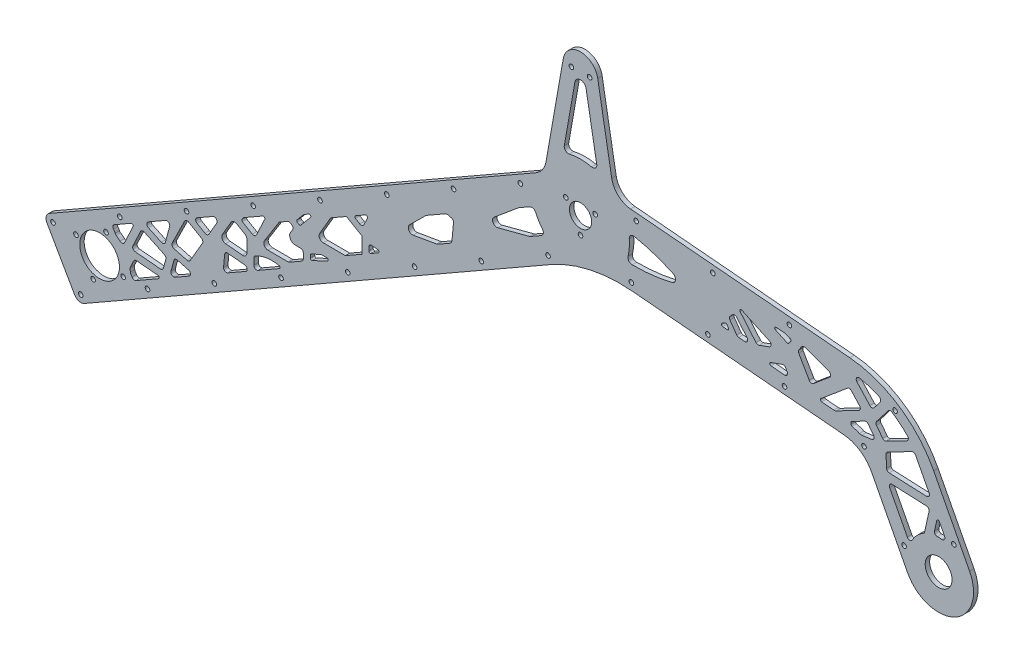
SolidWorks part; units mm, degrees
material "6061-T6 (SS)"
ref_plane "Front Plane" through (0, 0, 0) normal (0, 0, 1) x (1, 0, 0)
ref_plane "Top Plane" through (0, 0, 0) normal (0, 1, 0) x (1, 0, 0)
ref_plane "Right Plane" through (0, 0, 0) normal (1, 0, 0) x (0, 0, -1)
sketch "Reference Sketch" plane through (0, 0, 0) normal (0, 0, 1) x (1, 0, 0)
  line L0 (-343.92, -196.825) -> (0, 0) construction
  line L1 (-243.92, 103.175) -> (356.08, 103.175) construction
  line L2 (-243.92, 103.175) -> (-243.92, 0) construction
  line L3 (-243.92, 0) -> (356.08, 0) construction
  line L4 (356.08, 103.175) -> (356.08, 0) construction
  line L5 (0, 0) -> (256.08, -92.7116) construction
  line L6 (256.08, -92.7116) -> (56.08, -196.825) construction
  line L7 (256.08, -92.7116) -> (456.08, -196.825) construction
  line L8 (-343.92, -196.825) -> (56.08, -196.825) construction
  line L9 (56.08, -196.825) -> (456.08, -196.825) construction
  circle A1 centre (-343.92, -196.825) radius 100 construction
  circle A2 centre (56.08, -196.825) radius 100 construction
  circle A3 centre (456.08, -196.825) radius 100 construction
  circle A4 centre (-343.92, -196.825) radius 16.05 construction
  circle A5 centre (-343.92, -196.825) radius 28.55 construction
  circle A6 centre (-343.92, -196.825) radius 38.55 construction
  circle A7 centre (-343.92, -196.825) radius 33.55 construction
  point P13 (-343.92, -296.825)
  point P14 (556.08, -196.825)
  point P17 (-443.92, -196.825)
  dimension "D3" = 32.1
  dimension "D5" = 200
  dimension "D9" = 57.1
  dimension "D10" = 10
  dimension "D11" = 5
  dimension "D1" = 600
  dimension "D2" = 103.175
  dimension "D4" = 243.92
  dimension "D6" = 125
  dimension "D7" = 400
  dimension "D8" = 1000
  dimension "D12" = 356.08
sketch "Sketch2" plane through (0, 0, 0) normal (0, 0, 1) x (1, 0, 0)
  line L0 (-379.7168, -188.5069) -> (-32.0065, 10.4873)
  line L1 (-354.8814, -231.9028) -> (-21.5627, -41.1449)
  line L2 (-343.92, -196.825) -> (0, 0) construction
  line L3 (-184.3777, -76.7146) -> (-159.5423, -120.1104) construction
  line L4 (-24.685, 20.9013) -> (-12.3101, 91.0831)
  line L5 (12.3101, 91.0831) -> (22.322, 34.3028)
  line L6 (0, 98.4125) -> (0, 112.7) construction
  line L7 (-5.4848, 79.4125) -> (5.4848, 79.4125) construction
  line L8 (5.4848, 79.4125) -> (10.9697, 88.9125) construction
  line L9 (10.9697, 88.9125) -> (5.4848, 98.4125) construction
  line L10 (5.4848, 98.4125) -> (-5.4848, 98.4125) construction
  line L11 (-5.4848, 98.4125) -> (-10.9697, 88.9125) construction
  line L12 (-10.9697, 88.9125) -> (-5.4848, 79.4125) construction
  line L13 (-243.92, 103.175) -> (356.08, 103.175) construction
  line L14 (0, 88.9125) -> (0, 0) construction
  line L15 (35.7868, 21.9646) -> (192.5861, 8.2464)
  line L16 (252.5753, -31.8371) -> (278.2553, -81.1679)
  line L17 (233.9047, -104.2553) -> (208.2247, -54.9245)
  line L18 (36.8237, -28.3172) -> (188.2284, -41.5633)
  line L19 (0, 0) -> (192.5861, -16.8491) construction
  line L21 (-360.8064, -192.2315) -> (-339.3265, -179.9386) construction
  line L22 (-381.5729, -195.33) -> (-361.7045, -230.0467)
  line L23 (256.08, -92.7116) -> (56.08, -196.825) construction
  line L25 (-243.92, 0) -> (356.08, 0) construction
  circle A0 centre (0, 0) radius 7.9375
  circle A1 centre (-343.92, -196.825) radius 14.2
  arc A3 (-12.3101, 91.0831) -> (12.3101, 91.0831) centre (0, 88.9125) cw
  circle A4 centre (0, 88.9125) radius 6.5 construction
  circle A5 centre (-6.5, 88.9125) radius 1.65
  circle A6 centre (6.5, 88.9125) radius 1.65
  circle A7 centre (0, 88.9125) radius 9.5 construction
  arc A8 (252.5753, -31.8371) -> (192.5861, 8.2464) centre (186.0495, -66.4682) ccw
  circle A9 centre (256.08, -92.7116) radius 9.5885
  arc A10 (278.2553, -81.1679) -> (233.9047, -104.2553) centre (256.08, -92.7116) cw
  arc A11 (-21.5627, -41.1449) -> (36.8237, -28.3172) centre (28.1082, -127.9366) cw
  arc A12 (188.2284, -41.5633) -> (208.2247, -54.9245) centre (186.0495, -66.4682) cw
  arc A13 (22.322, 34.3028) -> (35.7868, 21.9646) centre (37.0941, 36.9075) ccw
  arc A14 (-32.0065, 10.4873) -> (-24.685, 20.9013) centre (-39.4572, 23.506) ccw
  circle A17 centre (-343.92, -196.825) radius 17.5 construction
  circle A18 centre (-360.8064, -192.2315) radius 1.65
  circle A19 centre (-339.3265, -179.9386) radius 1.65
  circle A20 centre (-327.0336, -201.4185) radius 1.65
  circle A21 centre (-348.5135, -213.7114) radius 1.65
  arc A27 (-379.7168, -188.5069) -> (-381.5729, -195.33) centre (-377.2333, -192.8465) ccw
  arc A28 (-361.7045, -230.0467) -> (-354.8814, -231.9028) centre (-357.3649, -227.5632) ccw
  circle A29 centre (-343.92, -196.825) radius 33.55 construction
  circle A32 centre (-343.92, -196.825) radius 38.55 construction
  point P16 (-171.96, -98.4125)
  point P64 (-343.92, -196.825)
  dimension "D1" = 15.875
  dimension "D2" = 28.4
  dimension "D3" = 35
  dimension "D5" = 13
  dimension "D6" = 3.3
  dimension "D7" = 6
  dimension "D12" = 50
  dimension "D14" = 100
  dimension "D16" = 15
  dimension "D17" = 5
  dimension "D18" = 25
  dimension "D19" = 3.3
  dimension "D15" = 4
  dimension "D20" = 19.177
  dimension "D4" = 50
  dimension "D8" = 19
  dimension "D9" = 14.2875
  dimension "D10" = 9.525
  dimension "D11" = 10
  dimension "D13" = 50
extrude "Base" add sketch "Sketch2" along normal blind 3.175
sketch "Sketch3" plane through (0, 0, 3.175) normal (0, 0, 1) x (1, 0, 0)
  line L0 (-343.92, -196.825) -> (0, 0) construction
  line L5 (0, 0) -> (197.3986, -17.2701) construction
  line L6 (192.5861, 8.2464) -> (35.7868, 21.9646) construction
  line L7 (0, 0) -> (-23.2167, -36.3305) construction
  line L8 (36.3074, -23.2529) -> (91.0981, -28.0464) construction
  line L9 (36.8237, -28.3172) -> (188.2284, -41.5633) construction
  line L10 (-357.3649, -227.5632) -> (-309.6295, -200.2442) construction
  line L11 (0, 0) -> (36.3074, -23.2529) construction
  line L12 (145.8888, -32.84) -> (188.6641, -36.5824) construction
  line L13 (149.375, 7.0078) -> (192.1504, 3.2654) construction
  line L14 (248.1402, -34.1458) -> (266.894, -70.1715) construction
  line L15 (278.2553, -81.1679) -> (252.5753, -31.8371) construction
  line L16 (212.6598, -52.6158) -> (231.4136, -88.6414) construction
  line L17 (208.2247, -54.9245) -> (233.9047, -104.2553) construction
  line L18 (231.4136, -88.6414) -> (266.894, -70.1715) construction
  circle A0 centre (-357.3649, -227.5632) radius 1.65
  circle A1 centre (-343.92, -196.825) radius 33.55 construction
  arc A2 (-361.7045, -230.0467) -> (-354.8814, -231.9028) centre (-357.3649, -227.5632) ccw construction
  circle A3 centre (-309.6295, -200.2442) radius 1.65
  circle A4 centre (-261.894, -172.9253) radius 1.65
  circle A5 centre (-214.1585, -145.6063) radius 1.65
  circle A6 centre (-166.4231, -118.2874) radius 1.65
  circle A7 centre (-118.6876, -90.9684) radius 1.65
  circle A8 centre (-329.4978, -165.5275) radius 1.65
  circle A9 centre (-377.2333, -192.8465) radius 1.65
  circle A10 centre (-281.7623, -138.2086) radius 1.65
  circle A11 centre (-234.0269, -110.8896) radius 1.65
  circle A12 centre (-186.2914, -83.5707) radius 1.65
  circle A13 centre (-138.5559, -56.2517) radius 1.65
  circle A14 centre (36.3074, -23.2529) radius 1.65
  circle A15 centre (91.0981, -28.0464) radius 1.65
  circle A16 centre (145.8888, -32.84) radius 1.65
  circle A17 centre (149.375, 7.0078) radius 1.65
  circle A18 centre (94.5843, 11.8013) radius 1.65
  circle A19 centre (39.7936, 16.5949) radius 1.65
  circle A20 centre (-70.9521, -63.6495) radius 1.65
  circle A21 centre (-23.2167, -36.3305) radius 1.65
  circle A22 centre (-43.085, -1.6138) radius 1.65
  circle A23 centre (-90.8205, -28.9328) radius 1.65
  arc A24 (188.6641, -36.5824) -> (212.6598, -52.6158) centre (186.0495, -66.4682) cw construction
  arc A25 (208.2247, -54.9245) -> (188.2284, -41.5633) centre (186.0495, -66.4682) ccw construction
  circle A26 centre (202.7166, -41.5241) radius 1.65
  arc A27 (192.1504, 3.2654) -> (248.1402, -34.1458) centre (186.0495, -66.4682) cw construction
  arc A28 (252.5753, -31.8371) -> (192.5861, 8.2464) centre (186.0495, -66.4682) ccw construction
  circle A29 centre (224.9394, -8.2653) radius 1.65
  circle A30 centre (231.4136, -88.6414) radius 1.65
  circle A31 centre (266.894, -70.1715) radius 1.65
  circle A32 centre (256.08, -92.7116) radius 9.5885 construction
  dimension "D1" = 3.3
  dimension "D2" = 8
  dimension "D3" = 5
  dimension "D5" = 3
  dimension "D6" = 15
  dimension "D4" = 55
extrude "Strut Holes" cut sketch "Sketch3" against normal through all
sketch "Sketch6" plane through (0, 0, 3.175) normal (0, 0, 1) x (1, 0, 0)
  line L0 (-317.9371, -199.2378) -> (-301.7593, -189.9792)
  line L1 (-354.8814, -231.9028) -> (-21.5627, -41.1449) construction
  line L2 (-289.845, -183.1607) -> (-279.9388, -177.4914)
  line L3 (-225.0683, -146.089) -> (-215.3943, -140.5526)
  line L4 (-202.4502, -105.5293) -> (-201.3111, -106.1928)
  line L5 (-333.4446, -172.395) -> (-321.3247, -165.4588)
  line L6 (-32.0065, 10.4873) -> (-379.7168, -188.5069) construction
  line L7 (-319.9233, -166.7528) -> (-326.0767, -179.819)
  line L8 (-329.2222, -183.6702) -> (-327.9453, -183.7868) construction
  line L9 (-302.165, -188.1154) -> (-317.5291, -186.7124)
  line L10 (-319.5204, -187.852) -> (-321.9207, -192.9489)
  line L11 (-296.5261, -175.2812) -> (-298.2962, -181.7883)
  line L12 (-300.4079, -183.2551) -> (-318.4265, -181.6097)
  line L13 (-320.054, -178.7659) -> (-314.5879, -167.159)
  line L14 (-311.9264, -166.2018) -> (-297.6038, -172.9468)
  line L15 (-280.4073, -173.8257) -> (-288.2923, -171.6808)
  line L16 (-290.7472, -173.0857) -> (-292.8686, -180.8843)
  line L17 (-296.7252, -151.3805) -> (-309.1621, -158.4982)
  line L18 (-309.0208, -162.0434) -> (-299.7125, -166.427)
  line L19 (-296.9305, -165.1426) -> (-293.8019, -153.6413)
  line L20 (-290.7492, -165.8308) -> (-281.4187, -168.3689)
  line L21 (-279.1655, -167.4456) -> (-270.335, -152.2839)
  line L22 (-271.0566, -149.5491) -> (-280.339, -144.1428)
  line L23 (-283.1398, -144.9875) -> (-292.0185, -163.0173)
  line L24 (-274.1749, -138.475) -> (-262.8296, -131.9821)
  line L25 (-260.108, -134.7245) -> (-265.8054, -144.5068)
  line L26 (-268.5402, -145.2285) -> (-274.188, -141.9391)
  line L27 (-255.2613, -159.7424) -> (-254.4886, -151.2802)
  line L28 (-252.315, -149.4703) -> (-240.2297, -150.5739)
  line L29 (-292.2711, -190.3101) -> (-299.0066, -188.4038) construction
  line L30 (-252.2762, -161.6601) -> (-239.4181, -154.3014)
  line L31 (-249.9491, -129.2039) -> (-256.1296, -139.8156)
  line L32 (-253.8101, -144.313) -> (-241.8428, -145.4058)
  line L33 (-238.5701, -142.4296) -> (-238.5385, -134.1139)
  line L34 (-240.0286, -131.5101) -> (-245.8469, -128.1214)
  line L35 (-233.5719, -142.9305) -> (-233.588, -147.1604)
  line L36 (-241.7536, -124.7193) -> (-234.6398, -128.8625)
  line L37 (-231.8238, -127.9864) -> (-225.7969, -115.1887)
  line L38 (-227.1983, -113.8948) -> (-240.4869, -121.4998)
  line L39 (-215.7001, -112.1928) -> (-226.033, -128.59)
  line L40 (-223.5063, -133.1894) -> (-209.2023, -133.2437)
  line L41 (-208.2012, -132.9795) -> (-199.2535, -127.8588)
  line L42 (-198.247, -126.1305) -> (-198.2324, -122.2852)
  line L43 (-200.2248, -120.2776) -> (-204.0086, -120.2632)
  line L44 (-207.3776, -114.1307) -> (-205.8611, -111.7242)
  line L45 (-206.5466, -108.9297) -> (-207.4931, -108.3784)
  line L46 (-209.4931, -108.3708) -> (-215.0015, -111.5233)
  line L47 (-220.5938, -138.2005) -> (-191.3457, -138.3115) construction
  line L48 (-200.0442, -105.9743) -> (-193.1087, -97.7724)
  line L49 (-194.3691, -96.2588) -> (-197.5103, -98.0565)
  line L50 (-198.0441, -98.501) -> (-202.7105, -104.0195)
  line L51 (-193.2277, -121.0545) -> (-193.2345, -122.8478)
  line L52 (-191.8153, -123.7595) -> (-180.9934, -118.7631)
  line L54 (-192.6468, -120.1504) -> (-185.8787, -117.0256)
  line L55 (-185.0328, -116.8414) -> (-181.4088, -116.8552)
  line L56 (-168.149, -108.9055) -> (-183.9527, -108.8455)
  line L57 (-186.5337, -104.3356) -> (-178.5799, -90.6792)
  line L58 (-178.5799, -90.6792) -> (-167.3868, -84.2735)
  line L59 (-167.3868, -84.2735) -> (-156.3884, -90.6792)
  line L60 (-156.3884, -90.6792) -> (-156.4321, -102.1999)
  line L61 (-156.4321, -102.1999) -> (-168.149, -108.9055)
  line L62 (-178.5799, -90.6792) -> (-168.149, -108.9055) construction
  line L63 (-151.4146, -97.6001) -> (-151.4054, -95.1814)
  line L64 (-149.2236, -93.1973) -> (-145.0326, -93.58)
  line L65 (-144.6268, -95.4437) -> (-149.9179, -98.4719)
  line L66 (-160.8726, -80.5454) -> (-153.7619, -76.4759)
  line L67 (-152.3605, -77.7699) -> (-154.93, -83.2262)
  line L68 (-157.746, -84.1023) -> (-160.8792, -82.2774)
  line L69 (-155.8599, -85.2008) -> (-151.3971, -92.9988) construction
  line L70 (-90.8199, -49.6985) -> (-91.8964, -61.4879)
  line L71 (-93.3939, -63.8188) -> (-101.9943, -68.7409)
  line L72 (-102.9747, -69.0935) -> (-119.6299, -71.9651)
  line L73 (-122.2529, -66.8794) -> (-110.6811, -55.3952)
  line L74 (-110.058, -54.9208) -> (-96.7247, -47.2901)
  line L75 (-94.4471, -46.9991) -> (-92.2866, -47.5868)
  line L76 (-102.4534, -69.0036) -> (-110.4008, -55.117) construction
  line L78 (-28.0968, -26.4494) -> (-35.8254, -30.8725)
  line L79 (-36.5501, -31.1694) -> (-59.134, -37.129)
  line L80 (-61.819, -31.9228) -> (-44.3172, -17.3499)
  line L81 (-43.8877, -17.0516) -> (-36.2746, -12.6946)
  line L82 (-44.1155, -17.182) -> (-36.1682, -31.0687) construction
  line L83 (-11.5997, 37.5245) -> (-3.9861, 80.7029)
  line L84 (3.9861, 80.7029) -> (11.5997, 37.5245)
  line L85 (22.322, 34.3028) -> (12.3101, 91.0831) construction
  line L86 (-12.3101, 91.0831) -> (-24.685, 20.9013) construction
  line L87 (192.5861, 8.2464) -> (35.7868, 21.9646) construction
  line L88 (36.8237, -28.3172) -> (188.2284, -41.5633) construction
  line L89 (-227.1773, -153.057) -> (-233.9128, -151.1507) construction
  line L90 (246.076, -72.9136) -> (249.254, -58.5784)
  line L91 (247.3887, -56.1475) -> (222.9622, -55.081)
  line L92 (221.1009, -58.0026) -> (233.7353, -82.273)
  line L93 (208.2247, -54.9245) -> (233.9047, -104.2553) construction
  line L94 (253.1337, -68.7997) -> (254.752, -61.5)
  line L95 (256.6153, -61.2547) -> (260.3456, -68.4206)
  line L96 (278.2553, -81.1679) -> (252.5753, -31.8371) construction
  line L97 (249.3108, -47.2228) -> (239.5975, -28.5637)
  line L98 (236.9, -27.7132) -> (219.5656, -36.7369)
  line L99 (218.491, -38.5982) -> (218.8608, -47.0688)
  line L100 (220.7717, -48.9796) -> (247.4495, -50.1444)
  line L101 (233.4135, -22.7639) -> (218.6181, -30.4658)
  line L102 (216.1079, -29.9093) -> (211.6718, -24.1281)
  line L103 (211.6718, -21.693) -> (220.0072, -10.8302)
  line L104 (209.6166, -31.3057) -> (205.7463, -26.2618)
  line L105 (203.2361, -25.7053) -> (194.0101, -30.5081)
  line L106 (193.4718, -31.3951) -> (193.4718, -32.4967)
  line L107 (201.069, -35.4569) -> (208.2909, -34.5061)
  line L108 (214.3031, -8.4078) -> (209.9577, -14.0708)
  line L109 (197.6887, -4.156) -> (206.8964, -14.2045)
  line L110 (193.6814, -11.6243) -> (199.5455, -18.0239)
  line L111 (198.9945, -21.1491) -> (182.8075, -29.5754)
  line L112 (181.1608, -29.903) -> (172.4826, -29.1438)
  line L113 (171.927, -27.3815) -> (190.9213, -11.4434)
  line L114 (178.1992, -11.0225) -> (166.5918, -20.7623)
  line L115 (163.5742, -20.2302) -> (156.048, -7.1944)
  line L116 (156.1417, -5.0472) -> (158.1885, -2.1242)
  line L117 (160.5108, -1.3919) -> (177.5977, -7.611)
  line L118 (146.6448, -20.9077) -> (147.747, -22.8167)
  line L119 (145.8406, -25.8091) -> (136.23, -24.9682)
  line L120 (135.9751, -23.0324) -> (144.2287, -20.0283)
  line L121 (134.9743, -13.819) -> (127.6718, -16.4769)
  line L122 (125.4557, -15.8831) -> (114.1985, -2.4673)
  line L123 (115.3872, -0.9182) -> (135.1355, -10.127)
  line L124 (139.4306, -1.096) -> (147.8318, -5.0136)
  line L125 (149.0736, -4.6809) -> (150.4259, -2.7496)
  line L126 (149.9488, -1.2363) -> (146.0985, 0.1651)
  line L127 (145.3339, 0.3346) -> (139.9404, 0.8065)
  line L128 (111.6605, -7.2212) -> (119.0455, -16.0223)
  line L129 (117.3391, -19.3002) -> (113.1162, -18.9308)
  line L130 (111.6522, -18.0855) -> (106.8775, -11.2665)
  line L131 (107.1016, -8.7052) -> (108.7142, -7.0926)
  line L132 (104.7039, -15.1361) -> (105.7554, -16.6377)
  line L133 (104.8491, -18.2075) -> (101.6773, -17.93)
  line L134 (101.2644, -16.0678) -> (103.3847, -14.8436)
  line L135 (-225.0683, -146.089) -> (-230.5959, -149.2525)
  line L136 (-233.5893, -147.5091) -> (-233.588, -147.1604)
  arc A0 (-320.7312, -198.3723) -> (-321.5152, -197.1118) centre (-327.0336, -201.4185) ccw
  arc A1 (-291.1568, -183.3993) -> (-291.2348, -183.3872) centre (-292.2711, -190.3101) ccw
  arc A2 (-225.7665, -146.2006) -> (-231.9116, -147.9008) centre (-227.1773, -153.057) ccw construction
  arc A4 (-321.937, -195.96) -> (-322.0953, -194.053) centre (-343.92, -196.825) ccw
  arc A5 (-332.8179, -177.3623) -> (-333.9791, -175.4215) centre (-339.3265, -179.9386) ccw
  arc A6 (-329.2222, -180.455) -> (-332.0384, -178.3094) centre (-343.92, -196.825) ccw
  arc A8 (-232.5183, -141.1762) -> (-215.6911, -138.7049) centre (-220.6887, -163.2003) cw
  arc A9 (-241.9747, -123.1658) -> (-241.1717, -122.1478) centre (-247.0456, -118.3403) ccw
  arc A10 (-32.0383, -14.0906) -> (-27.2511, -21.9631) centre (0, 0) ccw
  arc A11 (-256.1296, -139.8156) -> (-253.8101, -144.313) centre (-253.5373, -141.3254) ccw
  arc A12 (-226.033, -128.59) -> (-223.5063, -133.1894) centre (-223.4949, -130.1894) ccw
  arc A13 (-183.9527, -108.8455) -> (-186.5337, -104.3356) centre (-183.9413, -105.8455) cw
  arc A14 (-119.6299, -71.9651) -> (-122.2529, -66.8794) centre (-120.1396, -69.0087) cw
  arc A15 (-59.134, -37.129) -> (-61.819, -31.9228) centre (-59.8994, -34.2283) cw
  arc A16 (-7.9627, 34.0822) -> (7.9627, 34.0822) centre (0, 0) cw
  arc A17 (-3.9861, 80.7029) -> (3.9861, 80.7029) centre (0, 80) cw
  arc A18 (34.8636, 3.0867) -> (34.0029, -8.2948) centre (0, 0) cw
  arc A19 (38.4335, 6.2944) -> (66.0977, -2.7713) centre (15.1723, -111.4295) cw
  arc A20 (66.0977, -2.7713) -> (65.4856, -8.7407) centre (64.749, -5.6491) cw
  arc A21 (36.898, -12.0057) -> (65.4856, -8.7407) centre (37.6733, 107.9918) ccw
  arc A22 (245.141, -74.2025) -> (237.26, -82.3165) centre (256.08, -92.7116) ccw
  arc A23 (258.3595, -71.3328) -> (255.1708, -71.2308) centre (256.08, -92.7116) ccw
  arc A24 (222.6875, -10.3732) -> (233.9189, -19.5905) centre (186.0495, -66.4682) cw
  arc A25 (252.5753, -31.8371) -> (192.5861, 8.2464) centre (186.0495, -66.4682) ccw construction
  arc A26 (194.2312, -33.4673) -> (199.4914, -35.2382) centre (186.0495, -66.4682) cw
  arc A27 (208.2247, -54.9245) -> (188.2284, -41.5633) centre (186.0495, -66.4682) ccw construction
  arc A28 (213.5369, -5.3663) -> (199.5667, -0.8459) centre (186.0495, -66.4682) ccw
  arc A29 (218.8608, -47.0688) -> (220.7717, -48.9796) centre (220.8589, -46.9815) ccw
  arc A30 (239.5975, -28.5637) -> (236.9, -27.7132) centre (237.8235, -29.4872) ccw
  arc A31 (219.5656, -36.7369) -> (218.491, -38.5982) centre (220.4891, -38.5109) ccw
  arc A32 (127.6718, -16.4769) -> (125.4557, -15.8831) centre (126.9878, -14.5975) cw
  arc A33 (-240.4869, -121.4998) -> (-241.1717, -122.1478) centre (-239.4934, -123.2356) ccw
  arc A34 (-234.6398, -128.8625) -> (-231.8238, -127.9864) centre (-233.6332, -127.1343) ccw
  arc A35 (-233.5719, -142.9305) -> (-232.5183, -141.1762) centre (-231.5719, -142.9381) cw
  arc A36 (-317.9371, -199.2378) -> (-320.7312, -198.3723) centre (-318.9305, -197.5019) cw
  arc A37 (-321.937, -195.96) -> (-321.5152, -197.1118) centre (-319.9386, -195.8813) ccw
  arc A38 (-321.9207, -192.9489) -> (-322.0953, -194.053) centre (-320.1113, -193.801) ccw
  arc A39 (-317.5291, -186.7124) -> (-319.5204, -187.852) centre (-317.711, -188.7042) ccw
  arc A42 (-332.8179, -177.3623) -> (-332.0384, -178.3094) centre (-330.9583, -176.6261) ccw
  arc A43 (-333.4446, -172.395) -> (-333.9791, -175.4215) centre (-332.4512, -174.1309) ccw
  arc A44 (-318.4265, -181.6097) -> (-320.054, -178.7659) centre (-318.2446, -179.618) cw
  arc A45 (-298.2962, -181.7883) -> (-300.4079, -183.2551) centre (-300.226, -181.2634) cw
  arc A46 (-289.845, -183.1607) -> (-291.1568, -183.3993) centre (-290.8384, -181.4248) cw
  arc A47 (-292.8686, -180.8843) -> (-291.2348, -183.3872) centre (-290.9387, -181.4092) ccw
  arc A48 (-280.4073, -173.8257) -> (-279.9388, -177.4914) centre (-280.9322, -175.7556) cw
  arc A49 (-288.2923, -171.6808) -> (-290.7472, -173.0857) centre (-288.8173, -173.6107) ccw
  arc A50 (-296.5261, -175.2812) -> (-297.6038, -172.9468) centre (-298.456, -174.7562) ccw
  arc A51 (-314.5879, -167.159) -> (-311.9264, -166.2018) centre (-312.7785, -168.0112) cw
  arc A52 (-309.1621, -158.4982) -> (-309.0208, -162.0434) centre (-308.1687, -160.234) ccw
  arc A53 (-296.7252, -151.3805) -> (-293.8019, -153.6413) centre (-295.7318, -153.1164) cw
  arc A54 (-299.7125, -166.427) -> (-296.9305, -165.1426) centre (-298.8604, -164.6177) ccw
  arc A55 (-290.7492, -165.8308) -> (-292.0185, -163.0173) centre (-290.2242, -163.9009) cw
  arc A56 (-281.4187, -168.3689) -> (-279.1655, -167.4456) centre (-280.8937, -166.439) ccw
  arc A57 (-270.335, -152.2839) -> (-271.0566, -149.5491) centre (-272.0632, -151.2774) ccw
  arc A58 (-280.339, -144.1428) -> (-283.1398, -144.9875) centre (-281.3456, -145.8711) ccw
  arc A59 (-274.1749, -138.475) -> (-274.188, -141.9391) centre (-273.1814, -140.2108) ccw
  arc A60 (-265.8054, -144.5068) -> (-268.5402, -145.2285) centre (-267.5336, -143.5003) cw
  arc A61 (-254.4886, -151.2802) -> (-252.315, -149.4703) centre (-252.4969, -151.462) cw
  arc A62 (-255.2613, -159.7424) -> (-252.2762, -161.6601) centre (-253.2696, -159.9243) ccw
  arc A63 (-239.4181, -154.3014) -> (-240.2297, -150.5739) centre (-240.4115, -152.5656) ccw
  arc A64 (-262.8296, -131.9821) -> (-260.108, -134.7245) centre (-261.8362, -133.718) cw
  arc A65 (-209.2023, -133.2437) -> (-208.2012, -132.9795) centre (-209.1947, -131.2437) ccw
  arc A66 (-215.0015, -111.5233) -> (-215.7001, -112.1928) centre (-214.0081, -113.2591) ccw
  arc A67 (-207.4931, -108.3784) -> (-209.4931, -108.3708) centre (-208.4997, -110.1067) ccw
  arc A68 (-205.8611, -111.7242) -> (-206.5466, -108.9297) centre (-207.5531, -110.658) ccw
  arc A69 (-204.0086, -120.2632) -> (-207.3776, -114.1307) centre (-203.9934, -116.2633) cw
  arc A70 (-198.2324, -122.2852) -> (-200.2248, -120.2776) centre (-200.2323, -122.2776) ccw
  arc A71 (-199.2535, -127.8588) -> (-198.247, -126.1305) centre (-200.2469, -126.1229) ccw
  arc A72 (-185.8787, -117.0256) -> (-185.0328, -116.8414) centre (-185.0404, -118.8414) cw
  arc A73 (-197.5103, -98.0565) -> (-198.0441, -98.501) centre (-196.5169, -99.7924) ccw
  arc A74 (-151.4054, -95.1814) -> (-149.2236, -93.1973) centre (-149.4054, -95.189) cw
  arc A75 (-154.93, -83.2262) -> (-157.746, -84.1023) centre (-156.7394, -82.374) cw
  arc A76 (-90.8199, -49.6985) -> (-92.2866, -47.5868) centre (-92.8116, -49.5167) ccw
  arc A77 (111.6605, -7.2212) -> (108.7142, -7.0926) centre (110.1284, -8.5068) ccw
  arc A78 (106.8775, -11.2665) -> (107.1016, -8.7052) centre (108.5158, -10.1194) cw
  arc A79 (113.1162, -18.9308) -> (111.6522, -18.0855) centre (113.2905, -16.9384) cw
  arc A80 (119.0455, -16.0223) -> (117.3391, -19.3002) centre (117.5134, -17.3078) cw
  arc A81 (134.9743, -13.819) -> (135.1355, -10.127) centre (134.2903, -11.9396) ccw
  arc A82 (146.6448, -20.9077) -> (144.2287, -20.0283) centre (144.9128, -21.9077) ccw
  arc A83 (147.747, -22.8167) -> (145.8406, -25.8091) centre (146.0149, -23.8167) cw
  arc A84 (156.048, -7.1944) -> (156.1417, -5.0472) centre (157.78, -6.1944) cw
  arc A85 (158.1885, -2.1242) -> (160.5108, -1.3919) centre (159.8268, -3.2713) cw
  arc A86 (178.1992, -11.0225) -> (177.5977, -7.611) centre (176.9136, -9.4904) ccw
  arc A87 (166.5918, -20.7623) -> (163.5742, -20.2302) centre (165.3062, -19.2302) cw
  arc A88 (193.6814, -11.6243) -> (190.9213, -11.4434) centre (192.2068, -12.9755) ccw
  arc A89 (199.5455, -18.0239) -> (198.9945, -21.1491) centre (198.071, -19.375) cw
  arc A90 (209.9577, -14.0708) -> (206.8964, -14.2045) centre (208.371, -12.8533) cw
  arc A91 (213.5369, -5.3663) -> (214.3031, -8.4078) centre (212.7164, -7.1903) cw
  arc A92 (233.9189, -19.5905) -> (233.4135, -22.7639) centre (232.49, -20.9899) cw
  arc A93 (222.6875, -10.3732) -> (220.0072, -10.8302) centre (221.5939, -12.0477) ccw
  arc A94 (211.6718, -24.1281) -> (211.6718, -21.693) centre (213.2585, -22.9105) cw
  arc A95 (218.6181, -30.4658) -> (216.1079, -29.9093) centre (217.6946, -28.6918) cw
  arc A96 (205.7463, -26.2618) -> (203.2361, -25.7053) centre (204.1595, -27.4793) ccw
  arc A97 (209.6166, -31.3057) -> (208.2909, -34.5061) centre (208.0299, -32.5232) cw
  arc A98 (246.076, -72.9136) -> (245.141, -74.2025) centre (244.1234, -72.4807) cw
  arc A99 (249.254, -58.5784) -> (247.3887, -56.1475) centre (247.3014, -58.1456) ccw
  arc A100 (222.9622, -55.081) -> (221.1009, -58.0026) centre (222.8749, -57.0791) ccw
  arc A101 (233.7353, -82.273) -> (237.26, -82.3165) centre (235.5093, -81.3495) ccw
  arc A102 (260.3456, -68.4206) -> (258.3595, -71.3328) centre (258.5716, -69.344) cw
  arc A103 (253.1337, -68.7997) -> (255.1708, -71.2308) centre (255.0863, -69.2326) ccw
  arc A104 (249.3108, -47.2228) -> (247.4495, -50.1444) centre (247.5367, -48.1463) cw
  arc A105 (199.5667, -0.8459) -> (197.6887, -4.156) centre (199.1632, -2.8048) ccw
  arc A106 (-215.6911, -138.7049) -> (-215.3943, -140.5526) centre (-215.891, -139.6847) cw
  arc A107 (-301.7593, -189.9792) -> (-302.165, -188.1154) centre (-302.256, -189.1113) ccw
  arc A108 (-321.3247, -165.4588) -> (-319.9233, -166.7528) centre (-320.828, -166.3267) cw
  arc A109 (-225.7969, -115.1887) -> (-227.1983, -113.8948) centre (-226.7016, -114.7627) ccw
  arc A110 (-241.7536, -124.7193) -> (-241.9747, -123.1658) centre (-241.2503, -123.8551) cw
  arc A111 (-225.7665, -146.2006) -> (-225.0683, -146.089) centre (-225.565, -145.2211) ccw construction
  arc A112 (-233.588, -147.1604) -> (-231.9116, -147.9008) centre (-232.588, -147.1642) ccw construction
  arc A113 (-202.4502, -105.5293) -> (-202.7105, -104.0195) centre (-201.9469, -104.6652) cw
  arc A114 (-201.3111, -106.1928) -> (-200.0442, -105.9743) centre (-200.8078, -105.3286) ccw
  arc A115 (-193.2277, -121.0545) -> (-192.6468, -120.1504) centre (-192.2277, -121.0583) cw
  arc A116 (-193.2345, -122.8478) -> (-191.8153, -123.7595) centre (-192.2345, -122.8516) ccw
  arc A117 (-193.1087, -97.7724) -> (-194.3691, -96.2588) centre (-193.8723, -97.1267) ccw
  arc A118 (-180.9934, -118.7631) -> (-181.4088, -116.8552) centre (-181.4126, -117.8552) ccw
  arc A119 (-153.7619, -76.4759) -> (-152.3605, -77.7699) centre (-153.2652, -77.3438) cw
  arc A120 (-160.8726, -80.5454) -> (-160.8792, -82.2774) centre (-160.3759, -81.4133) ccw
  arc A121 (-151.4146, -97.6001) -> (-149.9179, -98.4719) centre (-150.4146, -97.6039) ccw
  arc A122 (-145.0326, -93.58) -> (-144.6268, -95.4437) centre (-145.1235, -94.5758) cw
  arc A123 (101.6773, -17.93) -> (101.2644, -16.0678) centre (101.7644, -16.9338) cw
  arc A124 (104.7039, -15.1361) -> (103.3847, -14.8436) centre (103.8847, -15.7096) ccw
  arc A125 (105.7554, -16.6377) -> (104.8491, -18.2075) centre (104.9362, -17.2113) cw
  arc A126 (114.1985, -2.4673) -> (115.3872, -0.9182) centre (114.9646, -1.8245) cw
  arc A127 (136.23, -24.9682) -> (135.9751, -23.0324) centre (136.3171, -23.972) cw
  arc A128 (139.4306, -1.096) -> (139.9404, 0.8065) centre (139.8532, -0.1897) cw
  arc A129 (172.4826, -29.1438) -> (171.927, -27.3815) centre (172.5698, -28.1476) cw
  arc A130 (194.0101, -30.5081) -> (193.4718, -31.3951) centre (194.4718, -31.3951) ccw
  arc A131 (193.4718, -32.4967) -> (194.2312, -33.4673) centre (194.4718, -32.4967) ccw
  arc A132 (254.752, -61.5) -> (256.6153, -61.2547) centre (255.7283, -61.7164) cw
  arc A133 (146.0985, 0.1651) -> (145.3339, 0.3346) centre (145.0724, -2.654) ccw
  arc A134 (199.4914, -35.2382) -> (201.069, -35.4569) centre (200.6774, -32.4826) ccw
  arc A135 (182.8075, -29.5754) -> (181.1608, -29.903) centre (181.4223, -26.9144) cw
  arc A136 (-7.9627, 34.0822) -> (-11.5997, 37.5245) centre (-8.6452, 37.0035) cw
  arc A137 (7.9627, 34.0822) -> (11.5997, 37.5245) centre (8.6452, 37.0035) ccw
  arc A138 (34.8636, 3.0867) -> (38.4335, 6.2944) centre (37.8519, 3.3513) cw
  arc A139 (34.0029, -8.2948) -> (36.898, -12.0057) centre (36.9174, -9.0058) ccw
  arc A140 (-35.8254, -30.8725) -> (-36.5501, -31.1694) centre (-37.3155, -28.2687) cw
  arc A141 (-44.3172, -17.3499) -> (-43.8877, -17.0516) centre (-42.3976, -19.6554) cw
  arc A142 (-32.0383, -14.0906) -> (-36.2746, -12.6946) centre (-34.7845, -15.2984) ccw
  arc A143 (-27.2511, -21.9631) -> (-28.0968, -26.4494) centre (-29.5869, -23.8456) cw
  arc A144 (-96.7247, -47.2901) -> (-94.4471, -46.9991) centre (-95.2346, -49.8939) cw
  arc A145 (-91.8964, -61.4879) -> (-93.3939, -63.8188) centre (-94.884, -61.2151) cw
  arc A146 (-110.6811, -55.3952) -> (-110.058, -54.9208) centre (-108.5679, -57.5245) cw
  arc A147 (-101.9943, -68.7409) -> (-102.9747, -69.0935) centre (-103.4845, -66.1371) cw
  arc A148 (-249.9491, -129.2039) -> (-245.8469, -128.1214) centre (-247.3568, -130.7138) cw
  arc A149 (-238.5385, -134.1139) -> (-240.0286, -131.5101) centre (-241.5385, -134.1025) ccw
  arc A150 (-241.8428, -145.4058) -> (-238.5701, -142.4296) centre (-241.57, -142.4182) ccw
  arc A151 (150.4259, -2.7496) -> (149.9488, -1.2363) centre (149.6067, -2.176) ccw
  arc A152 (147.8318, -5.0136) -> (149.0736, -4.6809) centre (148.2544, -4.1073) ccw
  arc A153 (-329.2222, -180.455) -> (-326.0767, -179.819) centre (-327.8861, -178.9669) ccw
  arc A154 (-230.5959, -149.2525) -> (-233.5893, -147.5091) centre (-231.5893, -147.5167) cw
  point P110 (-258.4996, -143.8848)
  point P113 (-228.9184, -133.1688)
  point P143 (34.9003, -2.6394)
  point P203 (218.9408, -48.8997)
  point P206 (238.674, -26.7897)
  point P211 (126.3559, -16.9559)
  point P214 (-240.9361, -121.7569)
  point P217 (-232.7537, -129.961)
  point P220 (-233.5675, -141.7728)
  point P229 (-318.9237, -186.5851)
  point P232 (-327.9453, -183.7868)
  point P235 (-326.0754, -183.9575)
  point P240 (-335.9304, -173.8176)
  point P247 (-290.5028, -183.5371)
  point P252 (-275.7482, -175.0931)
  point P255 (-290.2222, -171.1558)
  point P262 (-312.4966, -160.4065)
  point P265 (-292.5345, -148.9822)
  point P268 (-297.5562, -167.4426)
  point P271 (-293.0903, -165.1939)
  point P278 (-282.1923, -143.0634)
  point P281 (-277.1814, -140.1957)
  point P288 (-255.6107, -163.5684)
  point P294 (-256.3514, -128.2747)
  point P297 (-208.6664, -133.2457)
  point P300 (-215.4343, -111.7709)
  point P303 (-208.4909, -107.7973)
  point P308 (-211.2248, -120.2358)
  point P311 (-198.2248, -120.2852)
  point P314 (-198.2513, -127.2852)
  point P329 (110.2575, -5.5492)
  point P334 (112.1872, -18.8495)
  point P337 (122.1491, -19.721)
  point P340 (139.5116, -12.1676)
  point P345 (149.6679, -26.1439)
  point P350 (159.0687, -0.8671)
  point P353 (180.8529, -8.7958)
  point P356 (164.7659, -22.2944)
  point P363 (208.5067, -15.9618)
  point P366 (215.8118, -6.4415)
  point P369 (235.7568, -21.544)
  point P374 (210.7376, -22.9105)
  point P377 (217.1296, -31.2407)
  point P380 (204.7246, -24.9304)
  point P383 (211.7254, -34.054)
  point P390 (219.5014, -54.9299)
  point P393 (235.6626, -85.9753)
  point P396 (262.2729, -72.1228)
  point P401 (250.9103, -50.2955)
  point P406 (-213.2581, -139.3301)
  point P412 (-318.5721, -163.8835)
  point P415 (-224.4456, -112.3194)
  point P420 (-225.4089, -146.284)
  point P423 (-233.5998, -150.2728)
  point P426 (-203.48, -104.9295)
  point P431 (-193.2252, -120.4175)
  point P434 (-193.2404, -124.4175)
  point P437 (-189.4469, -93.4418)
  point P440 (-176.8981, -116.8723)
  point P447 (-151.4212, -99.3322)
  point P450 (-141.8741, -93.8684)
  point P453 (98.5177, -17.6536)
  point P458 (106.9854, -18.3944)
  point P463 (131.7364, -24.5751)
  point P468 (170.0776, -28.9333)
  point P471 (193.4718, -30.7883)
  point P474 (193.4718, -33.2883)
  point P477 (255.3467, -58.8176)
  point P484 (182.0319, -29.9792)
  point P491 (34.2849, 7.0387)
  point P494 (32.91, -11.9136)
  point P505 (-24.8853, -24.6115)
  point P508 (-95.6462, -46.6729)
  point P511 (-92.0384, -63.0431)
  point P524 (-238.5825, -145.7035)
  point P527 (151.1734, -1.682)
  point P530 (148.5923, -5.3682)
  dimension "D1" = 14
  dimension "D2" = 10
  dimension "D3" = 2
  dimension "D5" = 22
  dimension "D6" = 9
  dimension "D12" = 5
  dimension "D19" = 7
  dimension "D31" = 7
  dimension "D40" = 25
  dimension "D44" = 19
  dimension "D62" = 5
  dimension "D92" = 35
  dimension "D96" = 3
  dimension "D97" = 10
  dimension "D100" = 15
  dimension "D104" = 30
  dimension "D105" = 120
  dimension "D107" = 43
  dimension "D116" = 65
  dimension "D117" = 8
  dimension "D127" = 9
  dimension "D128" = 6
  dimension "D171" = 2
  dimension "D172" = 1
  dimension "D173" = 3
  dimension "D174" = 1
  dimension "D175" = 4
  dimension "D176" = 2
  dimension "D177" = 123.1958
  dimension "D183" = 7
  dimension "D184" = 2
  dimension "D7" = 35
  dimension "D8" = 35
  dimension "D9" = 20
  dimension "D10" = 22
  dimension "D11" = 20
  dimension "D13" = 5
  dimension "D14" = 45
  dimension "D15" = 45
  dimension "D16" = 17
  dimension "D17" = 15
  dimension "D18" = 5
  dimension "D20" = 55
  dimension "D21" = 5
  dimension "D22" = 45
  dimension "D23" = 23
  dimension "D24" = 34
  dimension "D25" = 60
  dimension "D26" = 5
  dimension "D27" = 5
  dimension "D28" = 5
  dimension "D29" = 30
  dimension "D30" = 24
  dimension "D32" = 55
  dimension "D33" = 35
  dimension "D34" = 25
  dimension "D35" = 5
  dimension "D36" = 6
  dimension "D37" = 60
  dimension "D38" = 5
  dimension "D39" = 20
  dimension "D41" = 11
  dimension "D42" = 35
  dimension "D43" = 60
  dimension "D45" = 19.5
  dimension "D46" = 5
  dimension "D47" = 5
  dimension "D48" = 30
  dimension "D49" = 5
  dimension "D50" = 14
  dimension "D51" = 13
  dimension "D52" = 8.5
  dimension "D53" = 60
  dimension "D54" = 12
  dimension "D55" = 7
  dimension "D56" = 22
  dimension "D57" = 28
  dimension "D58" = 60
  dimension "D59" = 15
  dimension "D60" = 8
  dimension "D61" = 13
  dimension "D63" = 12
  dimension "D64" = 20
  dimension "D65" = 5
  dimension "D66" = 65
  dimension "D67" = 25
  dimension "2" = 18
  dimension "D68" = 8
  dimension "D69" = 4
  dimension "D70" = 14
  dimension "D71" = 15
  dimension "D72" = 13.5
  dimension "D73" = 60
  dimension "D74" = 60
  dimension "D75" = 8
  dimension "D76" = 5
  dimension "D77" = 35
  dimension "D78" = 0.5076
  dimension "D79" = 5
  dimension "D80" = 11
  dimension "D81" = 35
  dimension "D82" = 16
  dimension "D83" = 18
  dimension "D84" = 55
  dimension "D85" = 45
  dimension "D86" = 20
  dimension "D87" = 15
  dimension "D88" = 12
  dimension "D89" = 17
  dimension "D90" = 16
  dimension "D91" = 18
  dimension "D93" = 15
  dimension "D94" = 10
  dimension "D95" = 13
  dimension "D98" = 10
  dimension "D99" = 80
  dimension "D101" = 16
  dimension "D102" = 22
  dimension "D103" = 22
  dimension "D106" = 7
  dimension "D108" = 10
  dimension "D109" = 40
  dimension "D110" = 10
  dimension "D111" = 6
  dimension "D112" = 60
  dimension "D113" = 35
  dimension "D114" = 15
  dimension "D115" = 6
  dimension "D118" = 26.5
  dimension "D119" = 6
  dimension "D120" = 85
  dimension "D121" = 85
  dimension "D122" = 32
  dimension "D123" = 21
  dimension "D124" = 80
  dimension "D125" = 75
  dimension "D126" = 6
  dimension "D129" = 10.5
  dimension "D130" = 80
  dimension "D131" = 12
  dimension "D132" = 8
  dimension "D133" = 6
  dimension "D134" = 2.5
  dimension "D135" = 100
  dimension "D136" = 11.5
  dimension "D137" = 60
  dimension "D138" = 11
  dimension "D139" = 45
  dimension "D140" = 12
  dimension "D141" = 8.5
  dimension "D142" = 12
  dimension "D143" = 18
  dimension "D144" = 80
  dimension "D145" = 21
  dimension "D146" = 60
  dimension "D147" = 60
  dimension "D148" = 15
  dimension "D149" = 12
  dimension "D150" = 18
  dimension "D151" = 25
  dimension "D152" = 9
  dimension "D153" = 12
  dimension "D154" = 6
  dimension "D155" = 15
  dimension "D156" = 20
  dimension "D157" = 10
  dimension "D158" = 13.5
  dimension "D159" = 4.5
  dimension "D160" = 45
  dimension "D161" = 14
  dimension "D162" = 5
  dimension "D163" = 10
  dimension "D164" = 16
  dimension "D165" = 50
  dimension "D166" = 18.5
  dimension "D167" = 50
  dimension "D168" = 4
  dimension "D169" = 8.5
  dimension "D170" = 35
  dimension "D178" = 124.6776
  dimension "D179" = 5
  dimension "D180" = 124.6776
  dimension "D181" = 5
  dimension "D182" = 36.4942
extrude "Lightening Holes" cut sketch "Sketch6" against normal through all
sketch "Sketch7" plane through (0, 0, 3.175) normal (0, 0, 1) x (1, 0, 0)
  circle A0 centre (-10.5, 6.0622) radius 1.65
  circle A1 centre (10.5, 6.0622) radius 1.65
  circle A2 centre (0, -12.1244) radius 1.65
  point P8 (0, 0)
  dimension "D1" = 3.3
  dimension "D3" = 21
  dimension "D2" = 3
extrude "Cut-Extrude1" cut sketch "Sketch7" against normal through all
